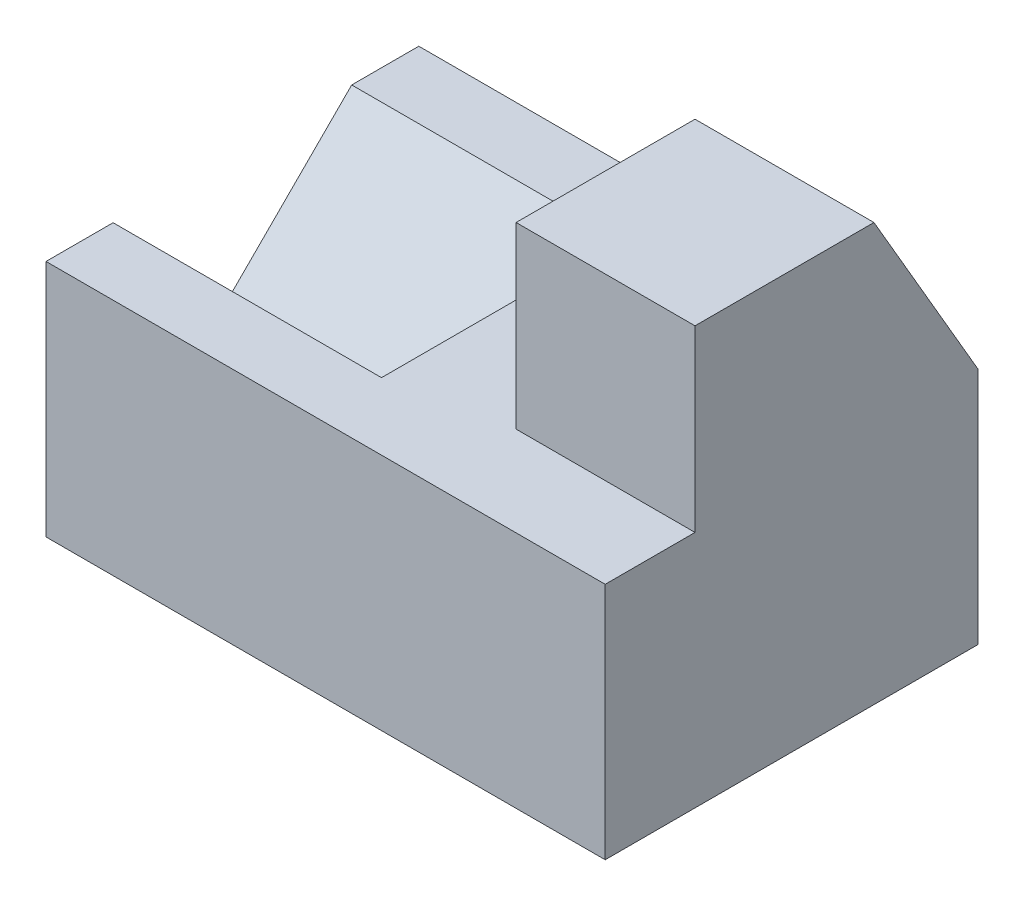
SolidWorks part; units mm, degrees
ref_plane "Front Plane" through (0, 0, 0) normal (0, 0, 1) x (1, 0, 0)
ref_plane "Top Plane" through (0, 0, 0) normal (0, 1, 0) x (1, 0, 0)
ref_plane "Right Plane" through (0, 0, 0) normal (1, 0, 0) x (0, 0, -1)
sketch "Sketch1" plane through (0, 0, 0) normal (1, 0, 0) x (0, 0, -1)
  line L0 (-9.8693, 13.856) -> (-9.8693, 37.856)
  line L1 (-21.9168, -18.144) -> (28.0832, -18.144)
  line L2 (-21.9168, -18.144) -> (-21.9168, 13.856)
  line L3 (-9.8693, 13.856) -> (28.0832, 13.856)
  line L4 (28.0832, -18.144) -> (28.0832, 13.856)
  line L5 (-9.8693, 37.856) -> (14.1307, 37.856)
  line L6 (14.1307, 37.856) -> (28.0832, 13.856)
  line L7 (-21.9168, 13.856) -> (-9.8693, 13.856)
  dimension "D3" = 24
  dimension "D1" = 50
  dimension "D2" = 32
  dimension "D4" = 24
  dimension "D5" = 12.0474
extrude "Boss-Extrude1" add sketch "Sketch1" against normal blind 75 contours L7 L2 L1 L4 L3 | L6 L5 L0 L3
sketch "Sketch2" plane through (-75, 0, 0) normal (-1, 0, 0) x (0, 0, 1)
  line L0 (-28.0832, 13.856) -> (9.8693, 13.856)
  line L1 (9.8693, 13.856) -> (9.8693, 37.856)
  line L2 (9.8693, 37.856) -> (-14.1307, 37.856)
  line L3 (-14.1307, 37.856) -> (-28.0832, 13.856)
extrude "Cut-Extrude1" cut sketch "Sketch2" against normal blind 51
sketch "Sketch3" plane through (-75, 0, 0) normal (-1, 0, 0) x (0, 0, 1)
  line L1 (-28.0832, 13.856) -> (9.8693, 13.856) construction
  line L4 (21.9168, 13.856) -> (-28.0832, 13.856) construction
  line L6 (-19.0832, 13.856) -> (12.9168, 13.856)
  line L7 (-19.0832, 13.856) -> (-3.0832, -2.144)
  line L8 (12.9168, 13.856) -> (-3.0832, -2.144)
extrude "Cut-Extrude2" cut sketch "Sketch3" against normal blind 36
